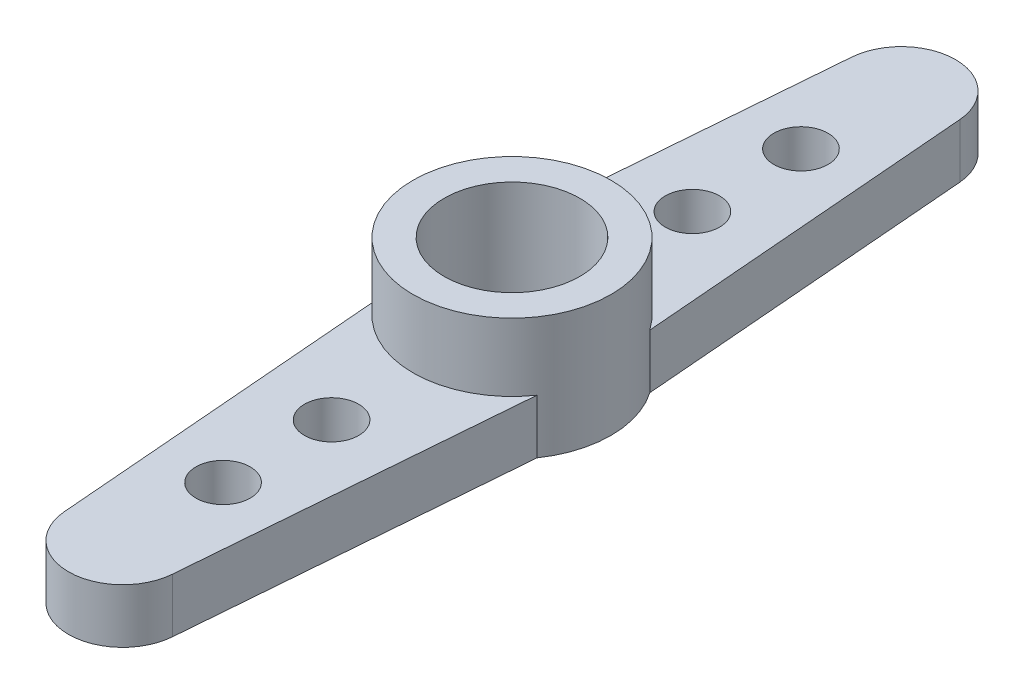
SolidWorks part; units mm, degrees
ref_plane "Front Plane" through (0, 0, 0) normal (0, 0, 1) x (1, 0, 0)
ref_plane "Top Plane" through (0, 0, 0) normal (0, 1, 0) x (1, 0, 0)
ref_plane "Right Plane" through (0, 0, 0) normal (1, 0, 0) x (0, 0, -1)
sketch "Sketch1" plane through (0, 0, 0) normal (0, 1, 0) x (1, 0, 0)
  line L0 (3, -2.0791) -> (1.9935, -14.5114)
  line L1 (-1.9935, -14.5114) -> (-3, -2.0791)
  arc A0 (3, -2.0791) -> (-3, -2.0791) centre (0, 0) ccw
  arc A1 (1.9935, -14.5114) -> (-1.9935, -14.5114) centre (0, -14.35) cw
  circle A2 centre (0, -6.65) radius 1
  circle A3 centre (0, -10.65) radius 1
  circle A4 centre (0, 0) radius 2.5
  dimension "D1" = 7.3
  dimension "D2" = 20
  dimension "D4" = 2
  dimension "D5" = 2
  dimension "D6" = 2
  dimension "D7" = 3
  dimension "D8" = 7
  dimension "D9" = 5
  dimension "D3" = 6
extrude "Boss-Extrude1" add sketch "Sketch1" along normal blind 2
sketch "Sketch2" plane through (0, 2, 0) normal (0, 1, 0) x (1, 0, 0)
  circle A0 centre (0, 0) radius 3.65
  circle A1 centre (0, 0) radius 2.5
extrude "Boss-Extrude2" add sketch "Sketch2" along normal blind 2.5
mirror "Mirror1" about plane through (0, 0, 0) normal (0, 0, 1) of "Boss-Extrude1", "Boss-Extrude2"
